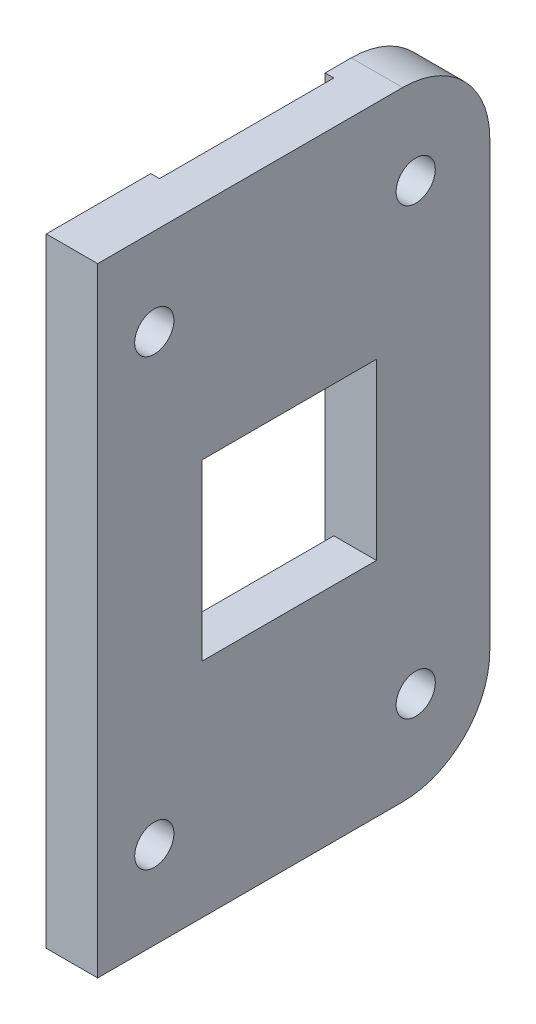
SolidWorks part; units mm, degrees
ref_plane "Front Plane" through (0, 0, 0) normal (0, 0, 1) x (1, 0, 0)
ref_plane "Top Plane" through (0, 0, 0) normal (0, 1, 0) x (1, 0, 0)
ref_plane "Right Plane" through (0, 0, 0) normal (1, 0, 0) x (0, 0, -1)
sketch "Sketch1" plane through (0, 0, 0) normal (0, 1, 0) x (1, 0, 0)
  line L0 (0, 24.8) -> (0, -20.2)
  line L4 (5.9, -20.2) -> (5.9, 24.8)
  line L5 (5.9, 24.8) -> (0, 24.8)
  line L6 (-5.9995, -20.2) -> (0.0005, -20.2) construction
  line L8 (0, -20.2) -> (5.9, -20.2)
extrude "Boss-Extrude1" add sketch "Sketch1" along normal blind 71
sketch "Sketch3" plane through (0, 0, 0) normal (0, -1, 0) x (1, 0, 0)
  line L0 (0, -24.8) -> (0, 20.2) construction
  line L1 (0, -11.8) -> (1, -11.8)
  line L2 (0, -11.8) -> (0, 8.2)
  line L3 (0, 8.2) -> (1, 8.2)
  line L4 (1, -11.8) -> (1, 8.2)
  line L5 (5.9, -24.8) -> (0, -24.8) construction
  dimension "D1" = 1
  dimension "D2" = 13
  dimension "D3" = 20
extrude "Cut-Extrude2" cut sketch "Sketch3" against normal up to next
fillet "Fillet1" radius 10 2 edges at (2.95, 0, -24.8) (2.95, 71, -24.8)
sketch "Sketch4" plane through (5.9, 0, 0) normal (1, 0, 0) x (0, 0, -1)
  circle A9 centre (-13.7, 61) radius 2.25 construction
  circle A10 centre (-13.7, 10) radius 2.25 construction
  circle A11 centre (16.3, 10) radius 2.25 construction
  circle A12 centre (16.3, 61) radius 2.25 construction
  circle A13 centre (-13.7, 61) radius 2.25
  circle A14 centre (-13.7, 10) radius 2.25
  circle A15 centre (16.3, 10) radius 2.25
  circle A16 centre (16.3, 61) radius 2.25
extrude "Cut-Extrude3" cut sketch "Sketch4" against normal up to next
sketch "Sketch5" plane through (5.9, 0, 0) normal (1, 0, 0) x (0, 0, -1)
  line L0 (11.8, 71) -> (11.8, 0) construction
  line L1 (11.8, 45.5) -> (-8.2, 45.5)
  line L2 (11.8, 45.5) -> (11.8, 25.5)
  line L3 (11.8, 25.5) -> (-8.2, 25.5)
  line L4 (-8.2, 45.5) -> (-8.2, 25.5)
  line L5 (-8.2, 71) -> (-8.2, 0) construction
  line L6 (24.8, 35.5) -> (-4.819, 35.5) construction
  line L7 (24.8, 61) -> (24.8, 10) construction
  point P10 (11.8, 35.5)
  dimension "D1" = 20
extrude "Cut-Extrude4" cut sketch "Sketch5" against normal up to next
